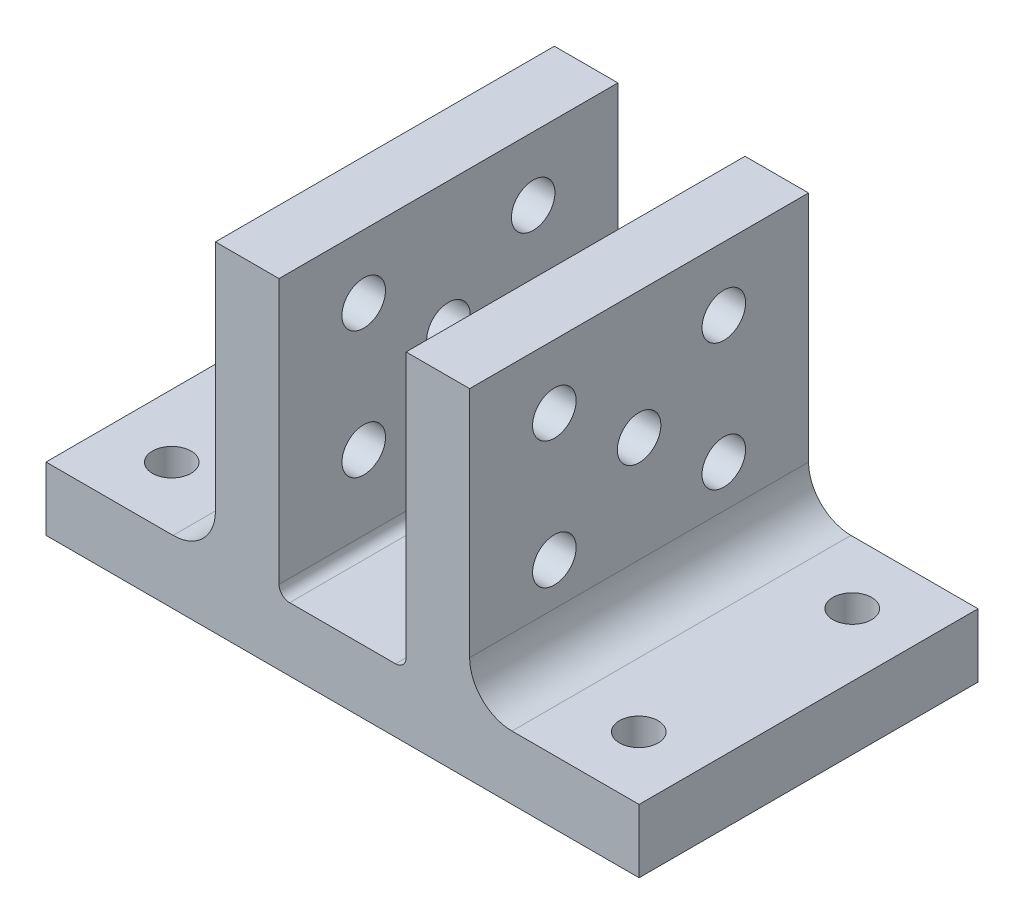
SolidWorks part; units mm, degrees
ref_plane "Front" through (0, 0, 0) normal (0, 0, 1) x (1, 0, 0)
ref_plane "Top" through (0, 0, 0) normal (0, 1, 0) x (1, 0, 0)
ref_plane "Right" through (0, 0, 0) normal (1, 0, 0) x (0, 0, -1)
sketch "Sketch1" plane through (0, 0, 0) normal (0, 0, 1) x (1, 0, 0)
  line L0 (-4.7625, 2.3812) -> (4.7625, 2.3812)
  line L1 (4.7625, 2.3812) -> (4.7625, 23.0187)
  line L2 (4.7625, 23.0187) -> (9.525, 23.0187)
  line L3 (9.525, 23.0187) -> (9.525, 5.5563)
  line L4 (12.7, 2.3812) -> (22.225, 2.3813)
  line L5 (22.225, 2.3813) -> (22.225, -2.3813)
  line L6 (22.225, -2.3813) -> (-22.225, -2.3813)
  line L7 (-22.225, -2.3813) -> (-22.225, 2.3812)
  line L8 (-22.225, 2.3812) -> (-12.7, 2.3812)
  line L9 (-9.525, 5.5563) -> (-9.525, 23.0187)
  line L10 (-9.525, 23.0187) -> (-4.7625, 23.0187)
  line L11 (-4.7625, 23.0187) -> (-4.7625, 2.3812)
  arc A0 (9.525, 5.5563) -> (12.7, 2.3812) centre (12.7, 5.5562) ccw
  arc A1 (-12.7, 2.3812) -> (-9.525, 5.5563) centre (-12.7, 5.5562) ccw
  point P13 (0, 2.3813)
  point P16 (0, -2.3813)
  point P18 (-22.225, 0)
  dimension "D6" = 3.175
  dimension "D1" = 4.7625
  dimension "D2" = 4.7625
  dimension "D3" = 44.45
  dimension "D4" = 9.525
  dimension "D5" = 25.4
extrude "Boss-Extrude1" add sketch "Sketch1" along normal blind 25.4
fillet "Fillet1" radius 0.7937 2 edges at (-4.7625, 2.3812, 12.7) (4.7625, 2.3812, 12.7)
hole_wizard "M2.5 Clearance Hole1" positions "Sketch2" profile "Sketch3" hole size "M2.5" standard "ANSI Metric" end condition through all
sketch "Sketch2" plane through (0, 2.3812, 0) normal (0, 1, 0) x (1, 0, 0)
  line L0 (22.225, -25.4) -> (22.225, 0) construction
  line L1 (-22.225, -25.4) -> (-22.225, 0) construction
  line L2 (17.5006, -20.6997) -> (17.5006, -4.7003) construction
  point P0 (17.5006, -4.7003)
  point P2 (17.5006, -20.6997)
  point P4 (-17.5006, -20.6997)
  point P6 (-17.5006, -4.7003)
  point P21 (17.5006, -12.7)
  point P22 (22.225, -12.7)
  dimension "D1" = 15.9995
  dimension "D2" = 4.7244
  dimension "D3" = 4.7244
sketch "Sketch3" plane through (17.5006, 2.3813, 4.7003) normal (1, 0, 0) x (0, 0, 1)
  line L0 (0, 0) -> (0, 4.7625)
  line L1 (0, 4.7625) -> (1.45, 4.7625)
  line L2 (1.45, 4.7625) -> (1.45, 0)
  line L5 (1.45, 0) -> (0, 0)
  line L11 (0, -6.35) -> (0, 107.95) construction
  dimension "Thru Hole Dia." = 2.9
  dimension "Thru Hole Depth" = 4.7625
hole_wizard "M2.5x0.45 Tapped Hole1" positions "Sketch4" profile "Sketch5" tap size "M2.5x0.45" standard "ANSI Metric"
sketch "Sketch4" plane through (0, -2.3813, 0) normal (0, -1, 0) x (-1, 0, 0)
  line L0 (-17.5006, -4.7003) -> (-7.78, -4.7003) construction
  line L2 (-17.5006, -20.6997) -> (7.78, -20.6997) construction
  circle A0 centre (-17.5006, -4.7003) radius 1.45 construction
  circle A1 centre (17.5006, -4.7003) radius 1.45 construction
  point P0 (-7.78, -4.7003)
  point P2 (7.78, -4.7003)
  point P4 (7.78, -20.6997)
  point P6 (-7.78, -20.6997)
  dimension "D1" = 9.7206
  dimension "D2" = 9.7206
sketch "Sketch5" plane through (7.78, -2.3813, 4.7003) normal (1, 0, 0) x (0, 0, -1)
  line L0 (0, 0) -> (0, 4.572)
  line L1 (0, 4.572) -> (1.025, 3.9561)
  line L2 (1.025, 3.9561) -> (1.025, 0)
  line L5 (1.025, 0) -> (0, 0)
  line L10 (0, 4.572) -> (-1.025, 3.9561) construction
  line L11 (0, -6.35) -> (0, 107.95) construction
  dimension "Tap Drill Dia." = 2.05
  dimension "Tap Drill Depth" = 4.572
  dimension "Drill Angle" = 118
hole_wizard "#4 Clearance Hole1" positions "Sketch6" profile "Sketch8" hole size "#4" standard "ANSI Inch" end condition through all
sketch "Sketch6" plane through (-9.525, 0, 0) normal (-1, 0, 0) x (0, 0, 1)
  line L0 (6.35, 18.2562) -> (6.35, 8.7312) construction
  line L2 (6.35, 18.2562) -> (19.05, 18.2562) construction
  line L4 (25.4, 23.0187) -> (0, 23.0187) construction
  line L6 (0, 5.5563) -> (0, 23.0187) construction
  line L7 (25.4, 2.3812) -> (0, 2.3812) construction
  point P0 (6.35, 18.2562)
  point P2 (19.05, 18.2562)
  point P4 (19.05, 8.7312)
  point P6 (6.35, 8.7312)
  point P8 (12.7, 13.4937)
  point P24 (12.7, 18.2562)
  point P28 (12.7, 23.0187)
  point P40 (6.35, 13.4937)
  dimension "D1" = 6.35
  dimension "D2" = 4.7625
  dimension "D3" = 6.35
sketch "Sketch8" plane through (-9.525, 18.2562, 6.35) normal (0, 1, 0) x (0, 0, 1)
  line L0 (0, 0) -> (0, 31.75)
  line L1 (0, 31.75) -> (1.6319, 31.75)
  line L2 (1.6319, 31.75) -> (1.6319, 0)
  line L5 (1.6319, 0) -> (0, 0)
  line L11 (0, -6.35) -> (0, 107.95) construction
  dimension "Thru Hole Dia." = 3.2639
  dimension "Thru Hole Depth" = 31.75
